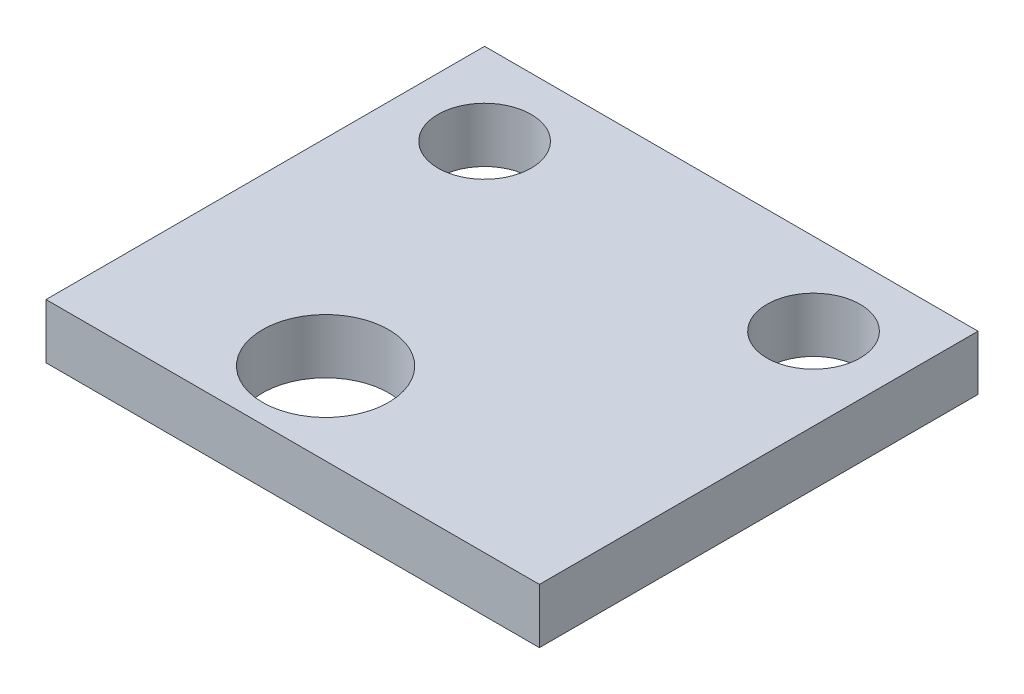
SolidWorks part; units mm, degrees
ref_plane "Спереди" through (0, 0, 0) normal (0, 0, 1) x (1, 0, 0)
ref_plane "Сверху" through (0, 0, 0) normal (0, 1, 0) x (1, 0, 0)
ref_plane "Справа" through (0, 0, 0) normal (1, 0, 0) x (0, 0, -1)
sketch "Эскиз1" plane through (0, 0, 0) normal (0, 1, 0) x (1, 0, 0)
  line L1 (0, 0) -> (9, 0)
  line L2 (0, 0) -> (0, 8)
  line L3 (0, 8) -> (9, 8)
  line L4 (9, 0) -> (9, 8)
  circle A0 centre (1.5, 6.5) radius 0.85
  circle A1 centre (7.5, 6.5) radius 0.85
  circle A2 centre (3.6, 1.5) radius 1.15
  dimension "D3" = 6
  dimension "D5" = 1.7
  dimension "D7" = 2.3
  dimension "D8" = 5
  dimension "D9" = 3.9
  dimension "D1" = 9
  dimension "D2" = 8
  dimension "D4" = 1.5
  dimension "D6" = 1.5
extrude "Бобышка-Вытянуть1" add sketch "Эскиз1" along normal blind 1
